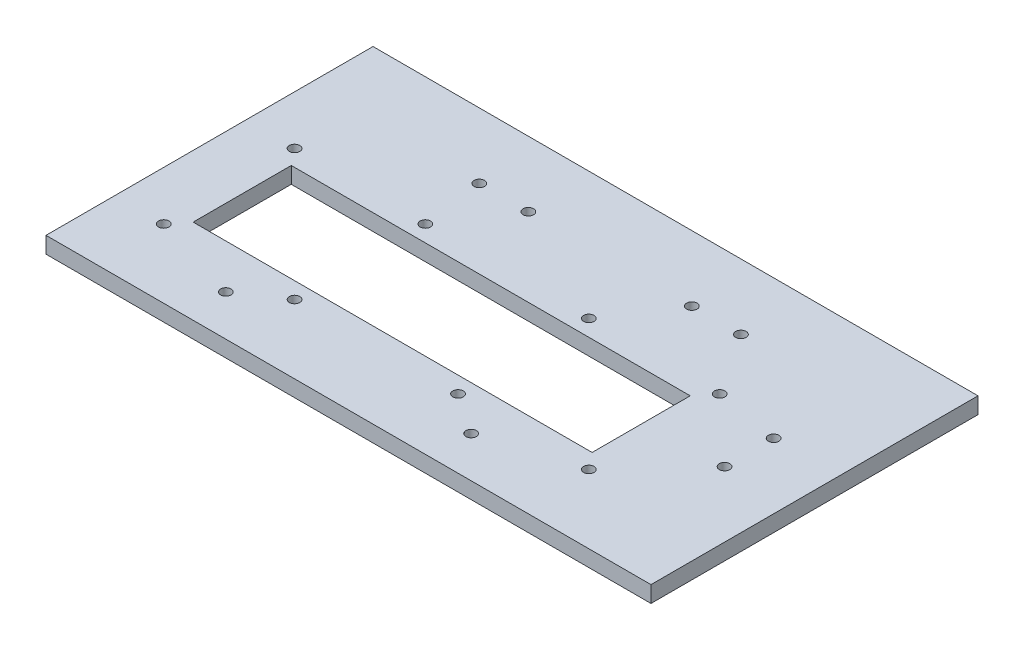
SolidWorks part; units mm, degrees
ref_plane "Front Plane" through (0, 0, 0) normal (0, 0, 1) x (1, 0, 0)
ref_plane "Top Plane" through (0, 0, 0) normal (0, 1, 0) x (1, 0, 0)
ref_plane "Right Plane" through (0, 0, 0) normal (1, 0, 0) x (0, 0, -1)
sketch "Sketch1" plane through (0, 0, 0) normal (0, 1, 0) x (1, 0, 0)
  line L0 (61, -15) -> (61, -41) construction
  line L1 (-61, -15) -> (61, -15)
  line L2 (-61, -15) -> (-61, 15)
  line L3 (-61, 15) -> (61, 15)
  line L4 (61, -15) -> (61, 15)
  line L5 (-61, -15) -> (61, 15) construction
  line L6 (-61, 15) -> (61, -15) construction
  line L11 (61, -41) -> (105, -41) construction
  line L12 (105, -41) -> (105, 59)
  line L13 (105, 59) -> (-80, 59)
  line L14 (105, -41) -> (-80, -41)
  line L15 (-80, -41) -> (-80, 59)
  point P0 (0, 0)
  point P6 (0, 0)
  dimension "D1" = 30
  dimension "D2" = 122
  dimension "D3" = 26
  dimension "D4" = 44
  dimension "D5" = 100
  dimension "D6" = 185
extrude "Boss-Extrude1" add sketch "Sketch1" along normal blind 5
sketch "Sketch2" plane through (0, 0, 0) normal (0, 1, 0) x (1, 0, 0)
  line L1 (25, -20) -> (-25, -20) construction
  line L2 (25, -20) -> (25, 20) construction
  line L3 (25, 20) -> (-25, 20) construction
  line L4 (-25, -20) -> (-25, 20) construction
  line L5 (25, -20) -> (-25, 20) construction
  line L6 (25, 20) -> (-25, -20) construction
  line L7 (65, -20) -> (-65, -20) construction
  line L8 (65, -20) -> (65, 20) construction
  line L9 (65, 20) -> (-65, 20) construction
  line L10 (-65, -20) -> (-65, 20) construction
  line L11 (65, -20) -> (-65, 20) construction
  line L12 (65, 20) -> (-65, -20) construction
  circle A0 centre (-25, 20) radius 1.6
  circle A1 centre (25, 20) radius 1.6
  circle A2 centre (25, -20) radius 1.6
  circle A3 centre (-25, -20) radius 1.6
  circle A4 centre (-65, 20) radius 1.6
  circle A5 centre (65, 20) radius 1.6
  circle A6 centre (65, -20) radius 1.6
  circle A7 centre (-65, -20) radius 1.6
  point P0 (0, 0)
  point P7 (0, 0)
  dimension "D3" = 3.2
  dimension "D8" = 3.2
  dimension "D1" = 50
  dimension "D2" = 40
  dimension "D6" = 130
  dimension "D7" = 40
  dimension "D4" = 2
  dimension "D5" = 2
  dimension "D9" = 2
  dimension "D10" = 2
extrude "Cut-Extrude2" cut sketch "Sketch2" along normal up to next
sketch "Sketch3" plane through (0, 5, 0) normal (0, 1, 0) x (1, 0, 0)
  line L0 (12.5, 59) -> (12.5, 39) construction
  line L1 (105, 59) -> (-80, 59) construction
  line L2 (12.5, 39) -> (-12.5, 39) construction
  line L3 (-12.5, 39) -> (-27.5, 39) construction
  circle A0 centre (-27.5, 39) radius 1.6
  circle A1 centre (-12.5, 39) radius 1.6
  circle A2 centre (37.5, 39) radius 1.6
  circle A3 centre (52.5, 39) radius 1.6
  dimension "D3" = 3.2
  dimension "D4" = 3.2
  dimension "D1" = 20
  dimension "D2" = 25
  dimension "D5" = 15
extrude "Cut-Extrude3" cut sketch "Sketch3" against normal up to next
sketch "Sketch4" plane through (0, 5, 0) normal (0, 1, 0) x (1, 0, 0)
  line L0 (0, -15) -> (0, -28.5) construction
  line L1 (-61, -15) -> (61, -15) construction
  line L2 (0, -28.5) -> (-37.5, -28.5) construction
  circle A0 centre (-37.5, -28.5) radius 1.6
  circle A1 centre (37.5, -28.5) radius 1.6
  dimension "D3" = 3.2
  dimension "D1" = 13.5
  dimension "D2" = 37.5
extrude "Cut-Extrude4" cut sketch "Sketch4" against normal up to next
sketch "Sketch5" plane through (0, 0, 0) normal (0, -1, 0) x (1, 0, 0)
  line L0 (100, 41) -> (100, -9) construction
  line L1 (100, -59) -> (100, 141) construction
  line L2 (100, -9) -> (85, -9) construction
  line L3 (85, -9) -> (85, -1.5) construction
  circle A0 centre (85, -1.5) radius 1.6
  circle A1 centre (85, -16.5) radius 1.6
  dimension "D4" = 3.2
  dimension "D1" = 50
  dimension "D2" = 15
  dimension "D3" = 7.5
extrude "Cut-Extrude5" cut sketch "Sketch5" against normal up to next
